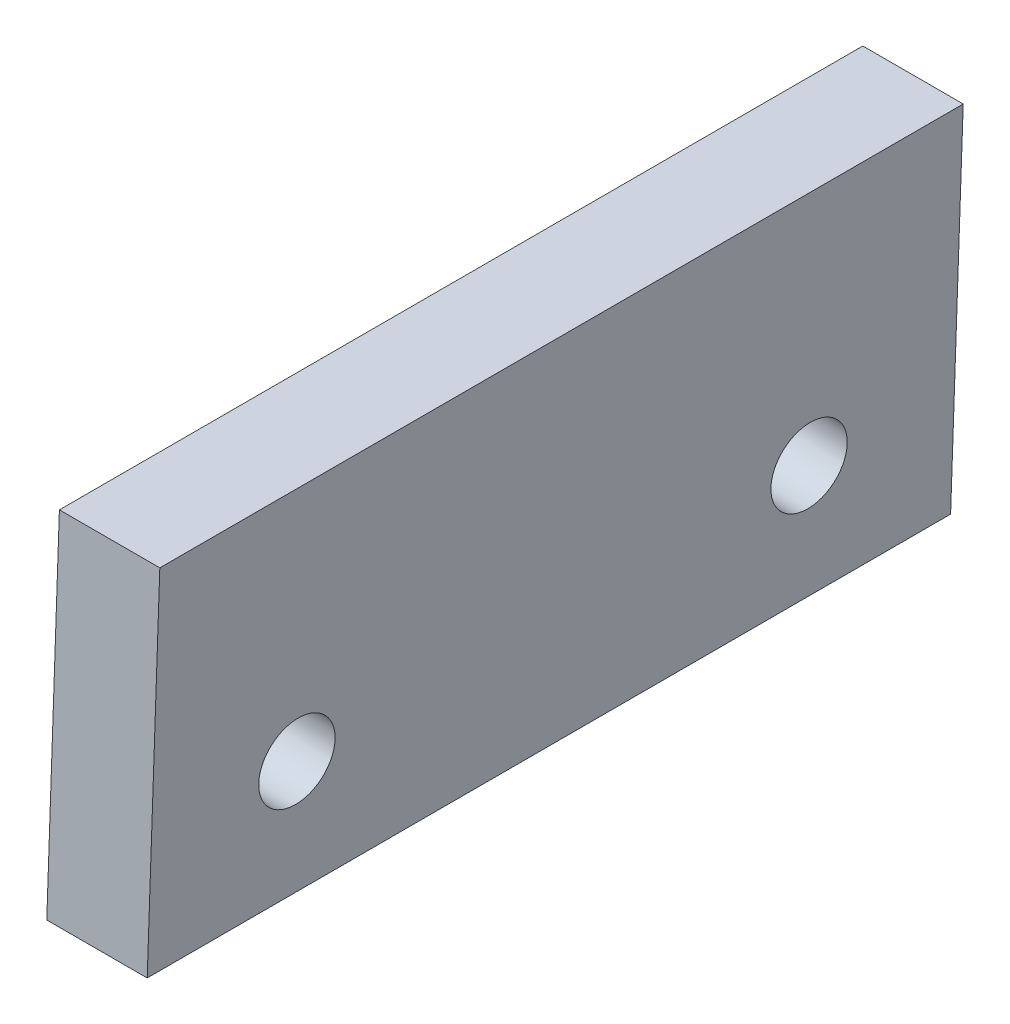
SolidWorks part; units mm, degrees
ref_plane "Front Plane" through (0, 0, 0) normal (0, 0, 1) x (1, 0, 0)
ref_plane "Top Plane" through (0, 0, 0) normal (0, 1, 0) x (1, 0, 0)
ref_plane "Right Plane" through (0, 0, 0) normal (1, 0, 0) x (0, 0, -1)
sketch "Sketch2" plane through (0, 0, 0) normal (0, 0, 1) x (1, 0, 0)
  line L0 (0, 0) -> (2.5, 0)
  line L1 (0, 0) -> (0.3143, 9)
  line L2 (2.5, 0) -> (2.8143, 9)
  line L3 (2.8143, 9) -> (0.3143, 9)
  line L4 (2.5, 0) -> (7.5011, 0) construction
  dimension "D1" = 9
  dimension "D2" = 2.5
  dimension "D3" = 88
extrude "Boss-Extrude2" add sketch "Sketch2" along normal blind 20
sketch "Sketch4" plane through (0, 0, 0) normal (-0.9994, 0.0349, 0) x (0, 0, 1)
  line L0 (0, 9.0055) -> (0, 0) construction
  line L1 (20, 9.0055) -> (20, 0) construction
  line L2 (20, 0) -> (0, 0) construction
  circle A0 centre (3.625, 3) radius 0.95
  circle A1 centre (16.375, 3) radius 0.95
  dimension "D1" = 3.625
  dimension "D2" = 3.625
  dimension "D3" = 3
  dimension "D4" = 3
  dimension "D5" = 1.9
  dimension "D6" = 1.9
extrude "Cut-Extrude1" cut sketch "Sketch4" against normal through all
